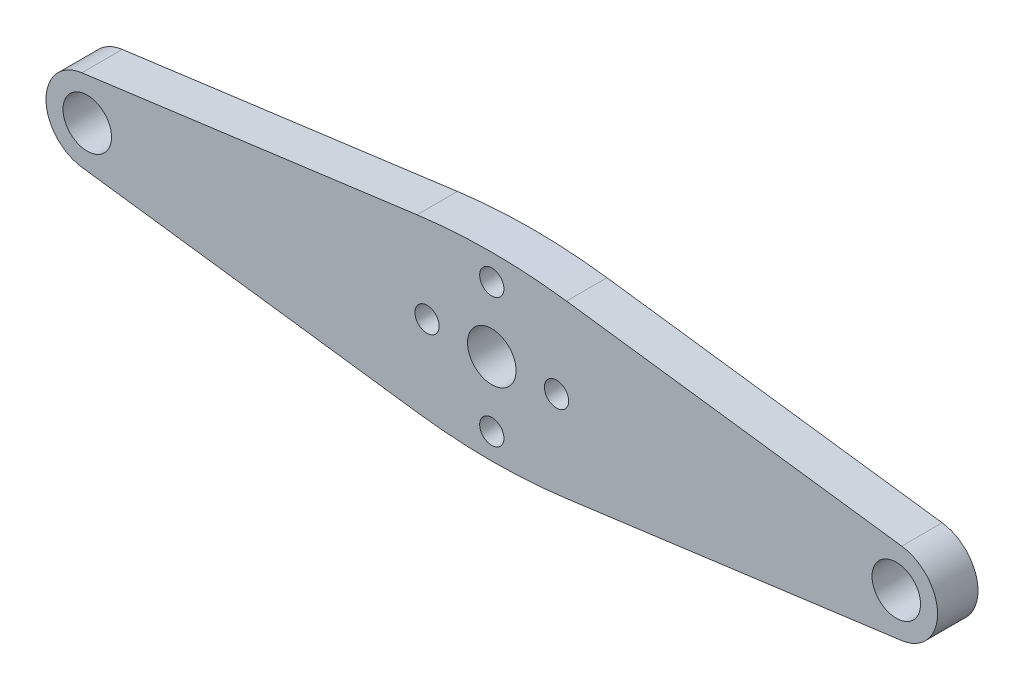
SolidWorks part; units mm, degrees
material "ABS"
ref_plane "Płaszczyzna przednia" through (0, 0, 0) normal (0, 0, 1) x (1, 0, 0)
ref_plane "Płaszczyzna górna" through (0, 0, 0) normal (0, 1, 0) x (1, 0, 0)
ref_plane "Płaszczyzna prawa" through (0, 0, 0) normal (1, 0, 0) x (0, 0, -1)
sketch "Szkic1" plane through (0, 0, 0) normal (0, 0, 1) x (1, 0, 0)
  line L0 (-44.521, 0) -> (57.4684, 0) construction
  line L1 (0, 0) -> (0, 26.3225) construction
  line L2 (-50.6729, 5.0557) -> (-9.2351, 10.5708)
  line L3 (-50.6729, -5.0557) -> (-9.2351, -10.5708)
  line L4 (50.6729, -5.0557) -> (9.2351, -10.5708)
  line L5 (50.6729, 5.0557) -> (9.2351, 10.5708)
  circle A0 centre (0, 0) radius 3
  circle A1 centre (0, 8) radius 1.5
  circle A2 centre (-8, 0) radius 1.5
  circle A3 centre (8, 0) radius 1.5
  circle A4 centre (0, -8) radius 1.5
  circle A5 centre (-50, 0) radius 3
  circle A6 centre (50, 0) radius 3
  arc A7 (-50.6729, 5.0557) -> (-50.6729, -5.0557) centre (-50, 0) ccw
  arc A8 (50.6729, 5.0557) -> (50.6729, -5.0557) centre (50, 0) cw
  arc A9 (-9.2351, 10.5708) -> (9.2351, 10.5708) centre (0, -58.8174) cw
  arc A10 (-9.2351, -10.5708) -> (9.2351, -10.5708) centre (0, 58.8174) ccw
  point P16 (0, 0)
  point P28 (0, 11.7999)
  point P31 (0, -11.7999)
  dimension "D1" = 4
  dimension "D2" = 50
  dimension "D3" = 6
  dimension "D4" = 6
  dimension "D5" = 3
  dimension "D6" = 16
  dimension "D7" = 70
extrude "Dodanie-wyciągnięcie1" add sketch "Szkic1" along normal blind 5
